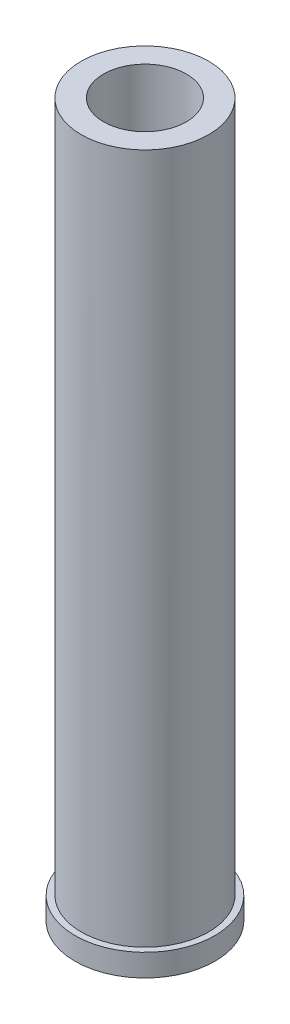
SolidWorks part; units mm, degrees
ref_plane "Front Plane" through (0, 0, 0) normal (0, 0, 1) x (1, 0, 0)
ref_plane "Top Plane" through (0, 0, 0) normal (0, 1, 0) x (1, 0, 0)
ref_plane "Right Plane" through (0, 0, 0) normal (1, 0, 0) x (0, 0, -1)
sketch "Sketch1" plane through (0, 0, 0) normal (0, 1, 0) x (1, 0, 0)
  circle A0 centre (0, 0) radius 14.3
  circle A1 centre (0, 0) radius 9.3
  dimension "D1" = 28.6
  dimension "D2" = 5
extrude "Boss-Extrude1" add sketch "Sketch1" along normal blind 160
sketch "Sketch2" plane through (0, 0, 0) normal (0, 0, 1) x (1, 0, 0)
  line L0 (-14.3, 160) -> (-14.3, 0) construction
  line L1 (-14.3, 3.6) -> (14.3, 3.6) construction
  line L2 (-14.3, 3.6) -> (-14.3, 1.4) construction
  line L3 (-14.3, 1.4) -> (14.3, 1.4) construction
  line L4 (14.3, 3.6) -> (14.3, 1.4) construction
  line L5 (0, 1.4) -> (0, 3.6) construction
  line L6 (-14.3, 2.5) -> (14.3, 2.5) construction
  line L7 (14.3, 0) -> (14.3, 160) construction
  line L8 (-15.7, 5) -> (-15.7, 0)
  line L9 (-15.7, 0) -> (15.7, 0)
  line L10 (15.7, 5) -> (15.7, 0)
  line L11 (-15.7, 5) -> (15.7, 5)
  line L12 (0, 300) -> (0, -49700) construction
  line L13 (9.3, 160) -> (-9.3, 160) construction
  line L14 (-14.3, 5) -> (-14.3, 0)
  point P16 (0, 160)
  point P220 (0, 2.5)
  dimension "D1" = 1.4
  dimension "D2" = 5
  dimension "D3" = 0
revolve "Revolve3" add sketch "Sketch2" angle 360 about L12
